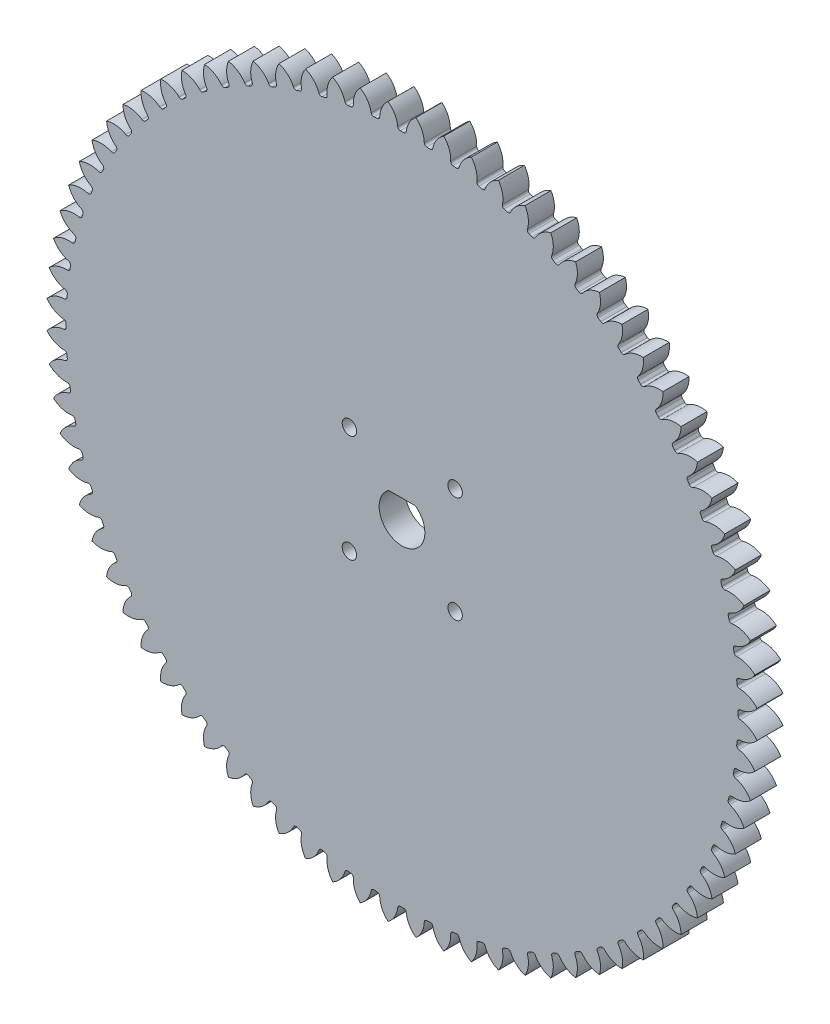
SolidWorks part; units mm, degrees
ref_plane "Front Plane" through (0, 0, 0) normal (0, 0, 1) x (1, 0, 0)
ref_plane "Top Plane" through (0, 0, 0) normal (0, 1, 0) x (1, 0, 0)
ref_plane "Right Plane" through (0, 0, 0) normal (1, 0, 0) x (0, 0, -1)
sketch "Sketch1" plane through (0, 0, 0) normal (0, 0, 1) x (1, 0, 0)
  circle A0 centre (0, 0) radius 120
  circle A1 centre (0, 0) radius 123
  dimension "D1" = 240
  dimension "D2" = 246
extrude "Boss-Extrude1" add sketch "Sketch1" along normal blind 9 contours A1 A0
sketch "Sketch2" plane through (0, 0, 9) normal (0, 0, 1) x (1, 0, 0)
  line L0 (0, 123) -> (0, 0) construction
  line L1 (0, 0) -> (9.6505, 122.6208) construction
  line L2 (0, 0) -> (4.829, 122.9052) construction
  line L3 (-1.4269, 116.2412) -> (0, 0) construction
  line L4 (-2.356, 119.9769) -> (2.356, 119.9769) construction
  line L5 (2.356, 119.9769) -> (7.0645, 119.7919) construction
  line L6 (-3.3685, 122.9539) -> (0, 113.6989) construction
  circle A0 centre (0, 0) radius 117 construction
  circle A2 centre (0, 0) radius 123 construction
  arc A3 (-4.856, 122.9041) -> (-1.4269, 116.2412) centre (-9.8145, 116.1383) cw
  circle A4 centre (0, 0) radius 123 construction
  arc A5 (4.856, 122.9041) -> (1.4269, 116.2412) centre (9.8145, 116.1383) ccw
  circle A6 centre (0, 0) radius 120 construction
  arc A7 (1.4269, 116.2412) -> (-1.4269, 116.2412) centre (0, 0) ccw
  circle M1 centre (0, 0) radius 123
  dimension "D1" = 4.5
  dimension "D2" = 6
  dimension "D4" = 20
  dimension "D3" = 0.75
extrude "Cut-Extrude1" cut sketch "Sketch2" against normal through all both and the other way through all contours A7 A5 A3 M1
fillet "Fillet1" radius 0.9 2 edges at (1.4269, 116.2412, 4.5) (-1.4269, 116.2412, 4.5)
pattern_circular "CirPattern3" count 80 over 360 about axis through (0, 0, 0) along (0, 0, 1) of "Fillet1", "Cut-Extrude1"
sketch "Sketch3" plane through (0, 0, 9) normal (0, 0, 1) x (1, 0, 0)
  point P6 (0, 5.975)
sketch "Sketch4" plane through (0, 0, 9) normal (0, 0, 1) x (1, 0, 0)
  line L0 (0, 0) -> (116.25, 0) construction
  line L1 (0, 0) -> (0.5769, 116.2486) construction
  line L2 (82.2012, 82.2012) -> (0, 0) construction
  arc A0 (116.2486, -0.5769) -> (116.2486, 0.5769) centre (0, 0) ccw construction
  circle A1 centre (0, 0) radius 116.25
  circle A2 centre (18.3848, 18.3848) radius 2.5
  circle A3 centre (-18.2014, 18.5663) radius 2.5
  circle A4 centre (-18.2014, -18.5663) radius 2.5
  circle A5 centre (18.3848, -18.3848) radius 2.5
  point P9 (82.2012, 82.2012)
  dimension "D3" = 5
  dimension "D1" = 45
  dimension "D2" = 26
extrude "Cut-Extrude3" cut sketch "Sketch4" against normal through all contours A3 | A5 | A4 | A2
sketch "Sketch5" plane through (0, 0, 9) normal (0, 0, 1) x (1, 0, 0)
  line L0 (-4.6363, 6.415) -> (4.6363, 6.415)
  arc A0 (-4.6363, 6.415) -> (4.6363, 6.415) centre (0, 0) ccw
  point P3 (0, 7.915)
  dimension "D1" = 15.83
  dimension "D2" = 1.5
extrude "Cut-Extrude4" cut sketch "Sketch5" against normal through all
fillet "Fillet2" radius 1 2 edges at (-4.6363, 6.415, 4.5) (4.6363, 6.415, 4.5)
equation "\"Module\"= 3mm"
equation "\"No. Teeth\"= 80"
equation "\"Contact Angle\"= 20"
equation "\"D1@Sketch1\"=\"Module\" * \"No. Teeth\""
equation "\"D2@Sketch1\"=(\"No. Teeth\" + 2) * \"Module\""
equation "\"D1@Sketch2\"=360/\"No. Teeth\""
equation "\"D2@Sketch2\"=2*\"Module\""
equation "\"D4@Sketch2\"=\"Contact Angle\""
equation "\"D1@Fillet1\"=0.3 * \"Module\""
equation "\"D1@CirPattern3\"=\"No. Teeth\""
